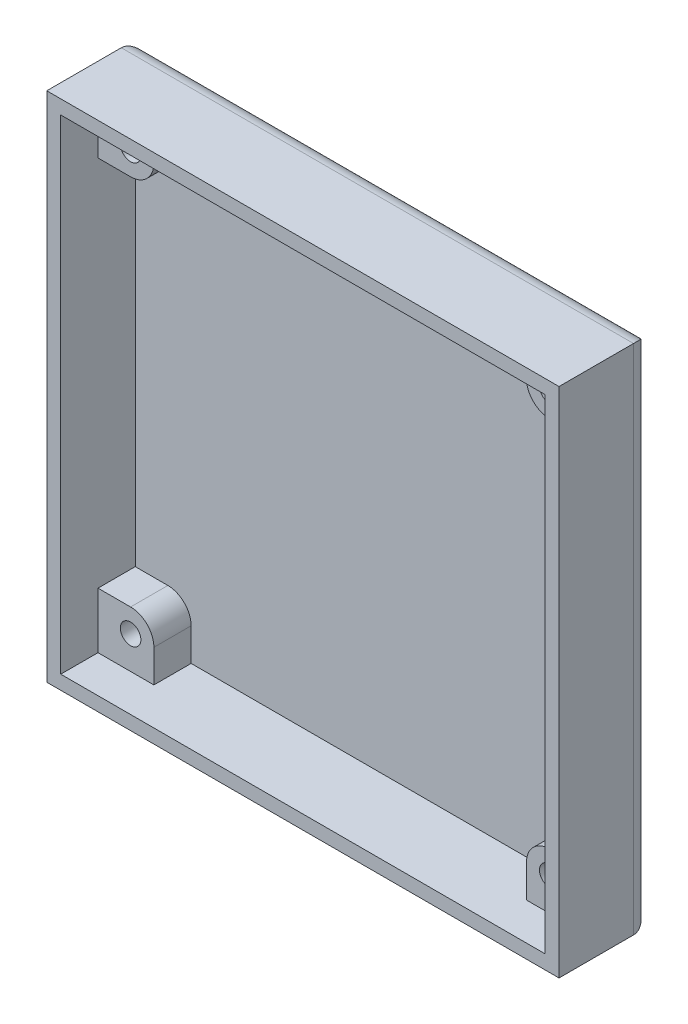
SolidWorks part; units mm, degrees
material "ABS"
ref_plane "前视基准面" through (0, 0, 0) normal (0, 0, 1) x (1, 0, 0)
ref_plane "上视基准面" through (0, 0, 0) normal (0, 1, 0) x (1, 0, 0)
ref_plane "右视基准面" through (0, 0, 0) normal (1, 0, 0) x (0, 0, -1)
other "Configuration Table"
sketch "草图1" plane through (0, 0, 0) normal (0, 0, 1) x (1, 0, 0)
  line L1 (-27.5, -27.5) -> (27.5, -27.5)
  line L2 (-27.5, -27.5) -> (-27.5, 27.5)
  line L3 (-27.5, 27.5) -> (27.5, 27.5)
  line L4 (27.5, -27.5) -> (27.5, 27.5)
  line L5 (-27.5, -27.5) -> (27.5, 27.5) construction
  line L6 (-27.5, 27.5) -> (27.5, -27.5) construction
  point P0 (0, 0)
extrude "凸台-拉伸1" add sketch "草图1" along normal blind 10
sketch "草图2" plane through (0, 0, 10) normal (0, 0, 1) x (1, 0, 0)
  line L1 (-26, -26) -> (26, -26)
  line L2 (-26, -26) -> (-26, 26)
  line L3 (-26, 26) -> (26, 26)
  line L4 (26, -26) -> (26, 26)
  line L5 (-26, -26) -> (26, 26) construction
  line L6 (-26, 26) -> (26, -26) construction
  point P0 (0, 0)
extrude "切除-拉伸1" cut sketch "草图2" against normal blind 8
fillet "圆角1" radius 2 4 edges at (27.5, 0, 0) (0, -27.5, 0) (-27.5, 0, 0) (0, 27.5, 0)
sketch "草图3" plane through (0, 0, 2) normal (0, 0, 1) x (1, 0, 0)
  line L5 (-22.5, -22.5) -> (22.5, -22.5) construction
  line L6 (-22.5, -22.5) -> (-22.5, 22.5) construction
  line L7 (-22.5, 22.5) -> (22.5, 22.5) construction
  line L8 (22.5, -22.5) -> (22.5, 22.5) construction
  line L9 (-22.5, -22.5) -> (22.5, 22.5) construction
  line L10 (-22.5, 22.5) -> (22.5, -22.5) construction
  circle A0 centre (-22.5, 22.5) radius 2.5
  circle A1 centre (22.5, 22.5) radius 2.5
  circle A2 centre (-22.5, -22.5) radius 2.5
  circle A3 centre (22.5, -22.5) radius 2.5
  point P0 (0, 0)
extrude "凸台-拉伸2" add sketch "草图3" along normal blind 4
sketch "草图5" plane through (0, 0, 6) normal (0, 0, 1) x (1, 0, 0)
  circle A0 centre (-22.5, -22.5) radius 1.1
  circle A1 centre (22.5, -22.5) radius 1.1
  circle A2 centre (-22.5, 22.5) radius 1.1
  circle A3 centre (22.5, 22.5) radius 1.1
extrude "切除-拉伸2" cut sketch "草图5" against normal blind 4
sketch "草图6" plane through (0, 0, 2) normal (0, 0, 1) x (1, 0, 0)
  line L0 (-22.5, 25) -> (-26, 25)
  line L1 (-25, 25) -> (-20, 25) construction
  line L2 (-25, 25) -> (-25, 20) construction
  line L3 (-25, 20) -> (-20, 20) construction
  line L4 (-20, 25) -> (-20, 20) construction
  line L5 (-25, 25) -> (-20, 20) construction
  line L6 (-25, 20) -> (-20, 25) construction
  line L7 (-26, 26) -> (-26, -26) construction
  line L8 (-26, 25) -> (-26, 20)
  line L9 (-26, 26) -> (-26, -26) construction
  line L10 (-26, 20) -> (-22.5, 20)
  circle A0 centre (-22.5, 22.5) radius 2.5 construction
  arc A1 (-22.5, 25) -> (-22.5, 20) centre (-22.5, 22.5) ccw
  point P0 (-22.5, 22.5)
extrude "凸台-拉伸4" add sketch "草图6" along normal blind 4
sketch "草图13" plane through (0, 0, 2) normal (0, 0, 1) x (1, 0, 0)
  line L0 (-20, 22.5) -> (-20, 26)
  line L1 (26, 26) -> (-26, 26) construction
  line L2 (-20, 26) -> (-26, 26)
  line L3 (26, 26) -> (-26, 26) construction
  line L4 (-26, 26) -> (-26, 25)
  line L5 (-26, 25) -> (-22.5, 25)
  line L6 (-22.5, -20) -> (-26, -20)
  line L7 (-26, 20) -> (-26, -26) construction
  line L8 (-26, -20) -> (-26, -26)
  line L9 (-26, -26) -> (-22.5, -26)
  line L10 (-26, -26) -> (26, -26) construction
  line L11 (-22.5, -26) -> (-20, -26)
  line L12 (-20, -26) -> (-20, -22.5)
  line L13 (22.5, -20) -> (26, -20)
  line L14 (26, -26) -> (26, 26) construction
  line L15 (26, -20) -> (26, -26)
  line L16 (26, -26) -> (20, -26)
  line L17 (20, -26) -> (20, -22.5)
  line L18 (20, 22.5) -> (20, 26)
  line L19 (20, 26) -> (26, 26)
  line L20 (26, 26) -> (26, 20)
  line L21 (26, 20) -> (22.5, 20)
  arc A0 (-22.5, 20) -> (-22.5, 25) centre (-22.5, 22.5) ccw construction
  arc A1 (-20, 22.5) -> (-22.5, 25) centre (-22.5, 22.5) ccw
  circle A2 centre (-22.5, -22.5) radius 2.5 construction
  circle A3 centre (-22.5, -22.5) radius 2.5 construction
  arc A4 (-22.5, -20) -> (-20, -22.5) centre (-22.5, -22.5) ccw
  circle A5 centre (22.5, -22.5) radius 2.5 construction
  circle A6 centre (22.5, -22.5) radius 2.5 construction
  arc A7 (22.5, -20) -> (20, -22.5) centre (22.5, -22.5) cw
  circle A8 centre (22.5, 22.5) radius 2.5 construction
  circle A9 centre (22.5, 22.5) radius 2.5 construction
  arc A10 (22.5, 20) -> (20, 22.5) centre (22.5, 22.5) ccw
  circle M1 centre (22.5, 22.5) radius 2.5
  circle M2 centre (-22.5, -22.5) radius 2.5
  circle M3 centre (22.5, -22.5) radius 2.5
  line M5 (-26, 20) -> (-26, -26)
  line M6 (-26, -26) -> (26, -26)
  line M7 (26, -26) -> (26, 26)
  line M8 (26, 26) -> (-26, 26)
  line M9 (-26, 26) -> (-26, 25)
  line M10 (-26, 25) -> (-22.5, 25)
  arc M11 (-22.5, 25) -> (-22.5, 20) centre (-22.5, 22.5) cw
extrude "凸台-拉伸6" add sketch "草图13" along normal blind 4 contours L21 L18 M7 M8 M1 | L0 M11 M8 M9 M10 | L12 L6 M6 M2 M5 | L17 L13 M6 M7 M3
sketch "草图15" plane through (0, 0, 6) normal (0, 0, 1) x (1, 0, 0)
  line L0 (-22.5, -22.5) -> (-26, -22.5) construction
  line L1 (-26, 26) -> (-26, -26) construction
sketch "草图16" plane through (-26, 0, 0) normal (1, 0, 0) x (0, 0, -1)
  line L0 (-6, -22.5) -> (-7.7, -22.5) construction
